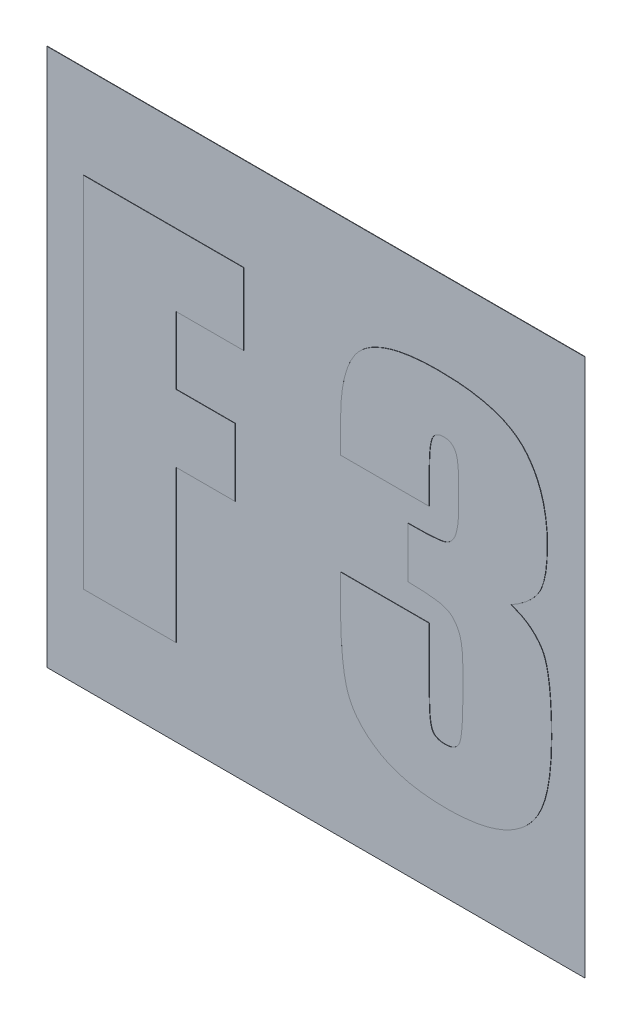
SolidWorks part; units mm, degrees
ref_plane "Plane1" through (0, 0, 0) normal (0, 0, 1) x (1, 0, 0)
ref_plane "Plane2" through (0, 0, 0) normal (0, 1, 0) x (1, 0, 0)
ref_plane "Plane3" through (0, 0, 0) normal (1, 0, 0) x (0, 0, -1)
sketch "Sketch1" plane through (0, 0, 0) normal (0, 0, 1) x (1, 0, 0)
  line L0 (-69.0098, 0) -> (69.0098, 0) construction
  line L1 (0, 52.3212) -> (0, -57.1323) construction
  line L2 (-7.5, 7.5) -> (7.5, 7.5)
  line L3 (-7.5, 7.5) -> (-7.5, -7.5)
  line L4 (7.5, 7.5) -> (7.5, -7.5)
  line L5 (-7.5, -7.5) -> (7.5, -7.5)
  point P8 (0, -7.5)
  point P11 (0, 7.5)
  point P12 (7.5, 0)
  point P13 (-7.5, 0)
  dimension "D1" = 15
  dimension "D2" = 15
extrude "Base-Extrude" add sketch "Sketch1" along normal blind 0.01
sketch "Sketch3" plane through (0, 0, 0.01) normal (0, 0, 1) x (1, 0, 0)
  text T0 "F 3" font "Impact" height in points 36
extrude "Boss-Extrude1" add sketch "Sketch3" along normal blind 0.01
